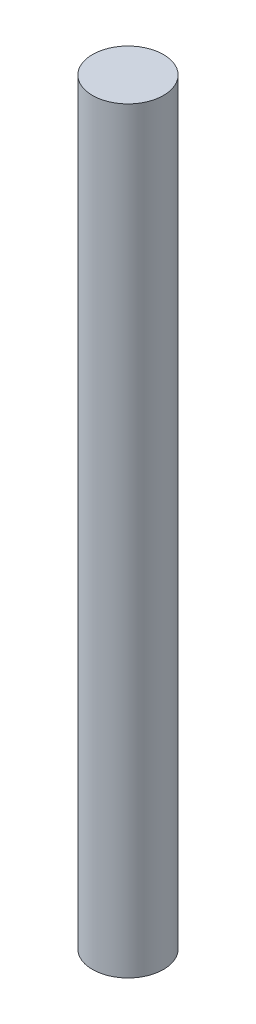
SolidWorks part; units mm, degrees
ref_plane "Front Plane" through (0, 0, 0) normal (0, 0, 1) x (1, 0, 0)
ref_plane "Top Plane" through (0, 0, 0) normal (0, 1, 0) x (1, 0, 0)
ref_plane "Right Plane" through (0, 0, 0) normal (1, 0, 0) x (0, 0, -1)
sketch "Sketch1" plane through (0, 0, 0) normal (0, 1, 0) x (1, 0, 0)
  circle A0 centre (0, 0) radius 2.3813
  dimension "D1" = 4.7625
extrude "Boss-Extrude1" add sketch "Sketch1" along normal blind 50.8
